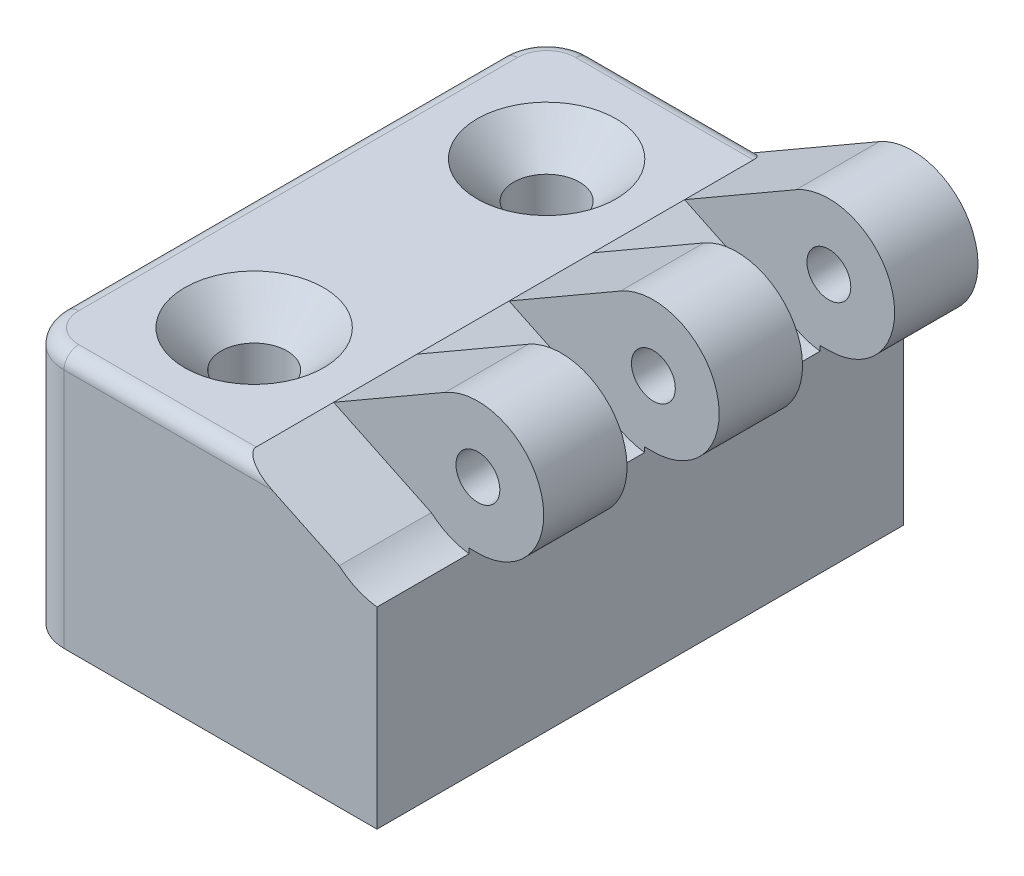
SolidWorks part; units mm, degrees
ref_plane "Front Plane" through (0, 0, 0) normal (0, 0, 1) x (1, 0, 0)
ref_plane "Top Plane" through (0, 0, 0) normal (0, 1, 0) x (1, 0, 0)
ref_plane "Right Plane" through (0, 0, 0) normal (1, 0, 0) x (0, 0, -1)
sketch "Croquis1" plane through (0, 0, 0) normal (0, 0, 1) x (1, 0, 0)
  line L0 (12.75, 7.8971) -> (5.134, 3.5)
  line L1 (-10, -4) -> (14.4, -4)
  line L2 (-10, -4) -> (-10, 3.5)
  line L3 (-10, 3.5) -> (5.134, 3.5)
  line L4 (15, -0.5) -> (14.4, -0.5)
  line L5 (-10, -4) -> (15, 4) construction
  line L6 (-10, 3.5) -> (18.6783, -4.5299) construction
  line L8 (14.4, -0.5) -> (14.4, -4)
  arc A0 (15, -0.5) -> (12.75, 7.8971) centre (15, 4) ccw
  circle A1 centre (15, 4) radius 1.5
  point P0 (2.5, 0)
  dimension "D3" = 3
  dimension "D4" = 4.5
  dimension "D1" = 7.5
  dimension "D2" = 25
  dimension "D5" = 30
  dimension "D6" = 0.6
  dimension "D7" = 3.5
extrude "Saliente-Extruir1" add sketch "Croquis1" against normal blind 36
sketch "Croquis2" plane through (0, 0, 0) normal (0, 0, 1) x (1, 0, 0)
  line L1 (14.4, -0.8426) -> (15, -0.5)
  line L2 (5.134, 3.5) -> (11.8076, 0.3095)
  line L3 (14.4, -4) -> (14.4, -0.5) construction
  line L5 (12.75, 7.8971) -> (5.134, 3.5) construction
  line L7 (12.75, 7.8971) -> (5.134, 3.5)
  arc A0 (15, -0.5) -> (12.75, 7.8971) centre (15, 4) ccw construction
  arc A1 (14.4, -0.8426) -> (11.8076, 0.3095) centre (15, 4) cw
  arc A2 (15, -0.5) -> (12.75, 7.8971) centre (15, 4) ccw
extrude "Cortar-Extruir1" cut sketch "Croquis2" against normal blind 6.3
pattern_linear "MatrizL1" count 3 spacing 12 along (0, 0, -1) of "Cortar-Extruir1"
sketch "Croquis3" plane through (0, 3.5, 0) normal (0, 1, 0) x (1, 0, 0)
  line L0 (-2, 28) -> (-2, 8) construction
  line L1 (5.134, 36) -> (-10, 36) construction
  line L2 (-10, 36) -> (-10, 0) construction
  circle A0 centre (-2, 28) radius 2.25
  circle A1 centre (-2, 8) radius 2.25
  dimension "D1" = 4.5
  dimension "D2" = 4.5
  dimension "D3" = 20
  dimension "D4" = 8
  dimension "D5" = 8
extrude "Cortar-Extruir2" cut sketch "Croquis3" against normal through all
chamfer "Chaflán1" distance 2.5 angle 45 2 edges at (-2, 3.5, -5.75) (-2, 3.5, -25.75)
fillet "Redondeo1" radius 3 2 edges at (-10, -0.25, 0) (-10, -0.25, -36)
fillet "Redondeo2" radius 1 5 edges at (-0.933, 3.5, -36) (-9.1213, 3.5, -35.1213) (-0.933, 3.5, 0) (-9.1213, 3.5, -0.8787) (-10, 3.5, -18)
sketch "Sketch1" plane through (0, -4, 0) normal (0, -1, 0) x (1, 0, 0)
  line L4 (-10, -3) -> (-10, -33)
  line L5 (-7, -36) -> (14.4, -36)
  line L6 (14.4, -36) -> (14.4, 0)
  line L7 (14.4, 0) -> (-7, 0)
  line L8 (-10, -3) -> (-10, -33)
  line L9 (-7, -36) -> (14.4, -36)
  line L10 (14.4, -36) -> (14.4, 0)
  line L11 (14.4, 0) -> (-7, 0)
  circle A0 centre (-2, -8) radius 2.25 construction
  circle A1 centre (-2, -8) radius 2.25
  arc A2 (-10, -33) -> (-7, -36) centre (-7, -33) ccw
  arc A3 (-7, 0) -> (-10, -3) centre (-7, -3) ccw
  arc A4 (-10, -33) -> (-7, -36) centre (-7, -33) ccw
  arc A5 (-7, 0) -> (-10, -3) centre (-7, -3) ccw
  circle A6 centre (-2, -28) radius 2.25 construction
  circle A7 centre (-2, -28) radius 2.25
  dimension "D1" = 0
extrude "Boss-Extrude2" add sketch "Sketch1" along normal blind 10
equation "\"num_dents\"= 3"
equation "\"gap\"= .6"
equation "\"llarg\"= 36"
equation "\"D1@Saliente-Extruir1\"=\"llarg\""
equation "\"D1@Cortar-Extruir1\"=(\"llarg\"-\"num_dents\"*\"gap\")/(2*\"num_dents\")+\"gap\""
equation "\"D1@MatrizL1\"=\"num_dents\""
equation "\"D3@MatrizL1\"=\"llarg\"/\"num_dents\""
equation "\"D2@Croquis3\"=\"D1@Croquis3\""
equation "\"D4@Croquis3\"=(\"llarg\"-\"D3@Croquis3\")/2"
equation "\"D5@Croquis3\"=\"D4@Croquis3\""
